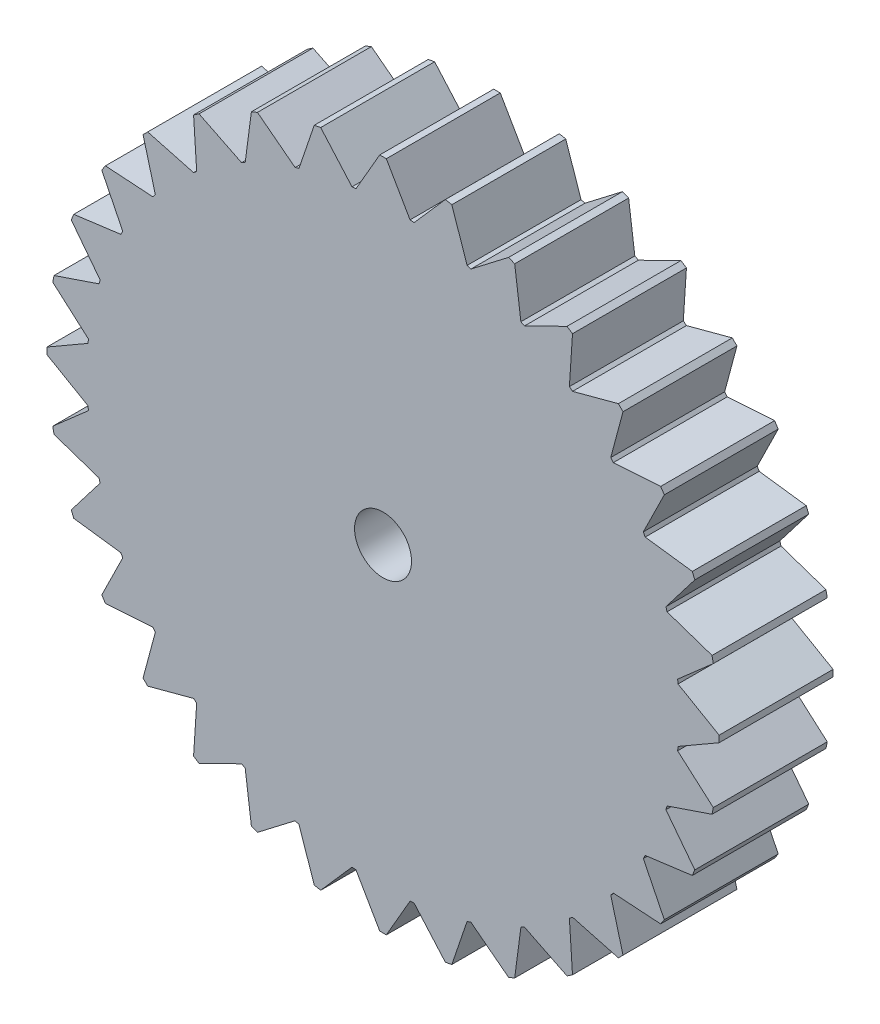
SolidWorks part; units mm, degrees
ref_plane "Front Plane" through (0, 0, 0) normal (0, 0, 1) x (1, 0, 0)
ref_plane "Top Plane" through (0, 0, 0) normal (0, 1, 0) x (1, 0, 0)
ref_plane "Right Plane" through (0, 0, 0) normal (1, 0, 0) x (0, 0, -1)
sketch "Sketch1" plane through (0, 0, 0) normal (0, 0, 1) x (1, 0, 0)
  line L0 (-28.9895, 5.472) -> (-25.8568, 2.7248)
  line L1 (-29.5, -0.2887) -> (-25.8916, -2.372)
  line L2 (-29.5, 0.2887) -> (-25.8916, 2.372)
  line L3 (-28.8768, 6.0383) -> (-28.9895, 5.472)
  line L4 (-29.5, 0) -> (-29.5, 0.2887)
  line L5 (-29.5, 0.2887) -> (-29.5, -0.2887)
  line L6 (-28.8768, 6.0383) -> (-24.9313, 7.3776)
  line L7 (-27.3649, 11.0225) -> (-24.8284, 7.7168)
  line L8 (-27.144, 11.5559) -> (-27.3649, 11.0225)
  line L9 (-27.144, 11.5559) -> (-23.013, 12.0997)
  line L10 (-24.6887, 16.1493) -> (-22.8459, 12.4123)
  line L11 (-24.368, 16.6293) -> (-24.6887, 16.1493)
  line L12 (-24.368, 16.6293) -> (-20.2102, 16.3568)
  line L13 (-21.0638, 20.6555) -> (-19.9854, 16.6308)
  line L14 (-20.6555, 21.0638) -> (-21.0638, 20.6555)
  line L15 (-20.6555, 21.0638) -> (-16.6308, 19.9854)
  line L16 (-16.6293, 24.368) -> (-16.3568, 20.2102)
  line L17 (-16.1493, 24.6887) -> (-16.6293, 24.368)
  line L18 (-16.1493, 24.6887) -> (-12.4123, 22.8459)
  line L19 (-11.5559, 27.144) -> (-12.0997, 23.013)
  line L20 (-11.0225, 27.3649) -> (-11.5559, 27.144)
  line L21 (-11.0225, 27.3649) -> (-7.7168, 24.8284)
  line L22 (-6.0383, 28.8768) -> (-7.3776, 24.9313)
  line L23 (-5.472, 28.9895) -> (-6.0383, 28.8768)
  line L24 (-5.472, 28.9895) -> (-2.7248, 25.8568)
  line L25 (-0.2887, 29.5) -> (-2.372, 25.8916)
  line L26 (0.2887, 29.5) -> (-0.2887, 29.5)
  line L27 (0.2887, 29.5) -> (2.372, 25.8916)
  line L28 (5.472, 28.9895) -> (2.7248, 25.8568)
  line L29 (6.0383, 28.8768) -> (5.472, 28.9895)
  line L30 (6.0383, 28.8768) -> (7.3776, 24.9313)
  line L31 (11.0225, 27.3649) -> (7.7168, 24.8284)
  line L32 (11.5559, 27.144) -> (11.0225, 27.3649)
  line L33 (11.5559, 27.144) -> (12.0997, 23.013)
  line L34 (16.1493, 24.6887) -> (12.4123, 22.8459)
  line L35 (16.6293, 24.368) -> (16.1493, 24.6887)
  line L36 (16.6293, 24.368) -> (16.3568, 20.2102)
  line L37 (20.6555, 21.0638) -> (16.6308, 19.9854)
  line L38 (21.0638, 20.6555) -> (20.6555, 21.0638)
  line L39 (21.0638, 20.6555) -> (19.9854, 16.6308)
  line L40 (24.368, 16.6293) -> (20.2102, 16.3568)
  line L41 (24.6887, 16.1493) -> (24.368, 16.6293)
  line L42 (24.6887, 16.1493) -> (22.8459, 12.4123)
  line L43 (27.144, 11.5559) -> (23.013, 12.0997)
  line L44 (27.3649, 11.0225) -> (27.144, 11.5559)
  line L45 (27.3649, 11.0225) -> (24.8284, 7.7168)
  line L46 (28.8768, 6.0383) -> (24.9313, 7.3776)
  line L47 (28.9895, 5.472) -> (28.8768, 6.0383)
  line L48 (28.9895, 5.472) -> (25.8568, 2.7248)
  line L49 (29.5, 0.2887) -> (25.8916, 2.372)
  line L50 (29.5, -0.2887) -> (29.5, 0.2887)
  line L51 (29.5, -0.2887) -> (25.8916, -2.372)
  line L52 (28.9895, -5.472) -> (25.8568, -2.7248)
  line L53 (28.8768, -6.0383) -> (28.9895, -5.472)
  line L54 (28.8768, -6.0383) -> (24.9313, -7.3776)
  line L55 (27.3649, -11.0225) -> (24.8284, -7.7168)
  line L56 (27.144, -11.5559) -> (27.3649, -11.0225)
  line L57 (27.144, -11.5559) -> (23.013, -12.0997)
  line L58 (24.6887, -16.1493) -> (22.8459, -12.4123)
  line L59 (24.368, -16.6293) -> (24.6887, -16.1493)
  line L60 (24.368, -16.6293) -> (20.2102, -16.3568)
  line L61 (21.0638, -20.6555) -> (19.9854, -16.6308)
  line L62 (20.6555, -21.0638) -> (21.0638, -20.6555)
  line L63 (20.6555, -21.0638) -> (16.6308, -19.9854)
  line L64 (16.6293, -24.368) -> (16.3568, -20.2102)
  line L65 (16.1493, -24.6887) -> (16.6293, -24.368)
  line L66 (16.1493, -24.6887) -> (12.4123, -22.8459)
  line L67 (11.5559, -27.144) -> (12.0997, -23.013)
  line L68 (11.0225, -27.3649) -> (11.5559, -27.144)
  line L69 (11.0225, -27.3649) -> (7.7168, -24.8284)
  line L70 (6.0383, -28.8768) -> (7.3776, -24.9313)
  line L71 (5.472, -28.9895) -> (6.0383, -28.8768)
  line L72 (5.472, -28.9895) -> (2.7248, -25.8568)
  line L73 (0.2887, -29.5) -> (2.372, -25.8916)
  line L74 (-0.2887, -29.5) -> (0.2887, -29.5)
  line L75 (-0.2887, -29.5) -> (-2.372, -25.8916)
  line L76 (-5.472, -28.9895) -> (-2.7248, -25.8568)
  line L77 (-6.0383, -28.8768) -> (-5.472, -28.9895)
  line L78 (-6.0383, -28.8768) -> (-7.3776, -24.9313)
  line L79 (-11.0225, -27.3649) -> (-7.7168, -24.8284)
  line L80 (-11.5559, -27.144) -> (-11.0225, -27.3649)
  line L81 (-11.5559, -27.144) -> (-12.0997, -23.013)
  line L82 (-16.1493, -24.6887) -> (-12.4123, -22.8459)
  line L83 (-16.6293, -24.368) -> (-16.1493, -24.6887)
  line L84 (-16.6293, -24.368) -> (-16.3568, -20.2102)
  line L85 (-20.6555, -21.0638) -> (-16.6308, -19.9854)
  line L86 (-21.0638, -20.6555) -> (-20.6555, -21.0638)
  line L87 (-21.0638, -20.6555) -> (-19.9854, -16.6308)
  line L88 (-24.368, -16.6293) -> (-20.2102, -16.3568)
  line L89 (-24.6887, -16.1493) -> (-24.368, -16.6293)
  line L90 (-24.6887, -16.1493) -> (-22.8459, -12.4123)
  line L91 (-27.144, -11.5559) -> (-23.013, -12.0997)
  line L92 (-27.3649, -11.0225) -> (-27.144, -11.5559)
  line L93 (-27.3649, -11.0225) -> (-24.8284, -7.7168)
  line L94 (-28.8768, -6.0383) -> (-24.9313, -7.3776)
  line L95 (-28.9895, -5.472) -> (-28.8768, -6.0383)
  line L96 (-28.9895, -5.472) -> (-25.8568, -2.7248)
  circle A1 centre (0, 0) radius 2.5
  arc A2 (-24.9313, -7.3776) -> (-24.8284, -7.7168) centre (0, 0) ccw
  arc A3 (-23.013, -12.0997) -> (-22.8459, -12.4123) centre (0, 0) ccw
  arc A4 (-20.2102, -16.3568) -> (-19.9854, -16.6308) centre (0, 0) ccw
  arc A5 (-16.6308, -19.9854) -> (-16.3568, -20.2102) centre (0, 0) ccw
  arc A6 (-12.4123, -22.8459) -> (-12.0997, -23.013) centre (0, 0) ccw
  arc A7 (-7.7168, -24.8284) -> (-7.3776, -24.9313) centre (0, 0) ccw
  arc A8 (-2.7248, -25.8568) -> (-2.372, -25.8916) centre (0, 0) ccw
  arc A9 (2.372, -25.8916) -> (2.7248, -25.8568) centre (0, 0) ccw
  arc A10 (7.3776, -24.9313) -> (7.7168, -24.8284) centre (0, 0) ccw
  arc A11 (12.0997, -23.013) -> (12.4123, -22.8459) centre (0, 0) ccw
  arc A12 (16.3568, -20.2102) -> (16.6308, -19.9854) centre (0, 0) ccw
  arc A13 (19.9854, -16.6308) -> (20.2102, -16.3568) centre (0, 0) ccw
  arc A14 (22.8459, -12.4123) -> (23.013, -12.0997) centre (0, 0) ccw
  arc A15 (24.8284, -7.7168) -> (24.9313, -7.3776) centre (0, 0) ccw
  arc A16 (25.8568, -2.7248) -> (25.8916, -2.372) centre (0, 0) ccw
  arc A17 (25.8916, 2.372) -> (25.8568, 2.7248) centre (0, 0) ccw
  arc A18 (24.9313, 7.3776) -> (24.8284, 7.7168) centre (0, 0) ccw
  arc A19 (23.013, 12.0997) -> (22.8459, 12.4123) centre (0, 0) ccw
  arc A20 (20.2102, 16.3568) -> (19.9854, 16.6308) centre (0, 0) ccw
  arc A21 (16.6308, 19.9854) -> (16.3568, 20.2102) centre (0, 0) ccw
  arc A22 (12.4123, 22.8459) -> (12.0997, 23.013) centre (0, 0) ccw
  arc A23 (7.7168, 24.8284) -> (7.3776, 24.9313) centre (0, 0) ccw
  arc A24 (2.7248, 25.8568) -> (2.372, 25.8916) centre (0, 0) ccw
  arc A25 (-2.372, 25.8916) -> (-2.7248, 25.8568) centre (0, 0) ccw
  arc A26 (-7.3776, 24.9313) -> (-7.7168, 24.8284) centre (0, 0) ccw
  arc A27 (-12.0997, 23.013) -> (-12.4123, 22.8459) centre (0, 0) ccw
  arc A28 (-16.3568, 20.2102) -> (-16.6308, 19.9854) centre (0, 0) ccw
  arc A29 (-19.9854, 16.6308) -> (-20.2102, 16.3568) centre (0, 0) ccw
  arc A30 (-22.8459, 12.4123) -> (-23.013, 12.0997) centre (0, 0) ccw
  arc A31 (-24.8284, 7.7168) -> (-24.9313, 7.3776) centre (0, 0) ccw
  arc A32 (-25.8568, 2.7248) -> (-25.8916, 2.372) centre (0, 0) ccw
  arc A33 (-25.8916, -2.372) -> (-25.8568, -2.7248) centre (0, 0) ccw
  point P137 (0, 0)
  dimension "D2" = 5
  dimension "D3" = 52
  dimension "D4" = 32
extrude "Boss-Extrude1" add sketch "Sketch1" along normal blind 10 contours L1 A33 L96 L95 L94 A2 L93 L92 L91 A3 L90 L89 L88 A4 L87 L86 L85 A5 L84 L83 L82 A6 L81 L80 L79 A7 L78 L77 L76 A8 L75 L74 L73 A9 L72 L71 L70 A10 L69 L68 L67 A11 L66 L65 L64 A12 L63 L62 L61 A13 L60
